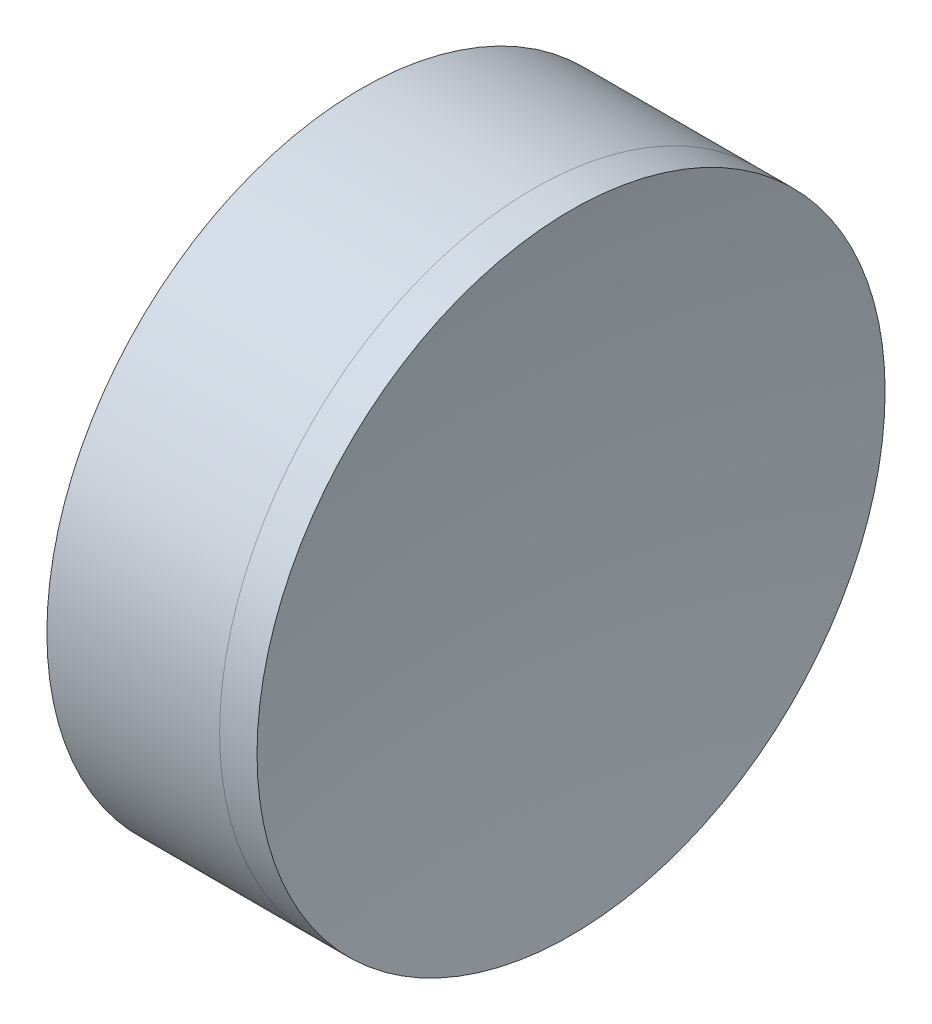
SolidWorks part; units mm, degrees
ref_plane "前视基准面" through (0, 0, 0) normal (0, 0, 1) x (1, 0, 0)
ref_plane "上视基准面" through (0, 0, 0) normal (0, 1, 0) x (1, 0, 0)
ref_plane "右视基准面" through (0, 0, 0) normal (1, 0, 0) x (0, 0, -1)
sketch "草图1" plane through (0, 0, 0) normal (0, 1, 0) x (1, 0, 0)
  line L0 (-0.8161, 0) -> (399.9621, 0) construction
  line L1 (250.6338, 20) -> (261.6345, 20)
  line L4 (250.6338, -20) -> (261.6345, -20)
  arc A0 (250.6338, -20) -> (250.6338, 20) centre (199.573, 0) ccw
  arc A1 (261.6345, 20) -> (261.6345, -20) centre (297.311, 0) ccw
  point P6 (254.411, 0)
  point P8 (256.411, 0)
  dimension "D3" = 20
  dimension "D4" = 2
  dimension "D1" = 54.838
  dimension "D5" = 40.9
  dimension "D2" = 20
revolve "旋转1" add sketch "草图1" angle 360 about L0
sketch "草图2" plane through (0, 0, 0) normal (0, 1, 0) x (1, 0, 0)
  line L2 (250.6338, 0) -> (272.9951, 0) construction
  line L3 (250.6338, -20) -> (250.6338, 20) construction
  line L6 (261.6345, 20) -> (264.0155, 20)
  line L7 (261.6345, -20) -> (264.0155, -20)
  arc A2 (261.6345, 20) -> (261.6345, -20) centre (297.311, 0) ccw construction
  arc A3 (261.6345, 20) -> (261.6345, -20) centre (297.311, 0) ccw
  arc A4 (264.0155, 20) -> (264.0155, -20) centre (387.861, 0) ccw
  point P8 (256.411, 0)
  point P9 (262.411, 0)
  dimension "D1" = 6
  dimension "D2" = 125.45
revolve "旋转3" add sketch "草图2" angle 360 about L2
